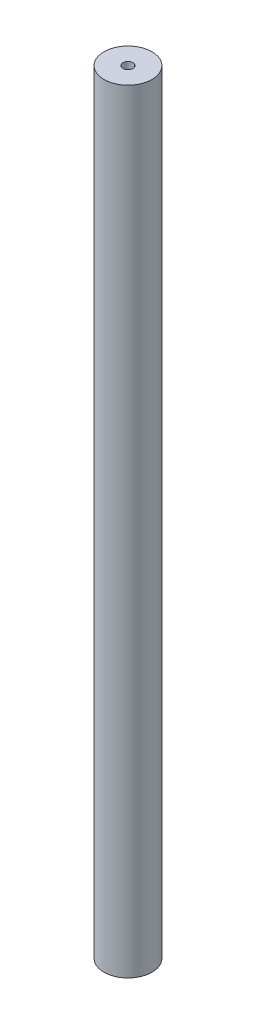
SolidWorks part; units mm, degrees
ref_plane "Front Plane" through (0, 0, 0) normal (0, 0, 1) x (1, 0, 0)
ref_plane "Top Plane" through (0, 0, 0) normal (0, 1, 0) x (1, 0, 0)
ref_plane "Right Plane" through (0, 0, 0) normal (1, 0, 0) x (0, 0, -1)
sketch "Sketch1" plane through (0, 0, 0) normal (0, 1, 0) x (1, 0, 0)
  circle A0 centre (0, 0) radius 10
  dimension "D1" = 20
extrude "Boss-Extrude1" add sketch "Sketch1" along normal mid plane 322.2
hole_wizard "M5x0.8 Tapped Hole1" positions "Sketch2" profile "Sketch3" tap size "M5x0.8" standard "ANSI Metric"
sketch "Sketch2" plane through (0, 161.1, 0) normal (0, 1, 0) x (1, 0, 0)
  point P0 (0, 0)
sketch "Sketch3" plane through (0, 161.1, 0) normal (1, 0, 0) x (0, 0, 1)
  line L0 (0, 0) -> (0, 23.7618)
  line L1 (0, 23.7618) -> (2.1, 22.5)
  line L2 (2.1, 22.5) -> (2.1, 0)
  line L5 (2.1, 0) -> (0, 0)
  line L10 (0, 23.7618) -> (-2.1, 22.5) construction
  line L11 (0, -6.35) -> (0, 107.95) construction
  dimension "Tap Drill Dia." = 4.2
  dimension "Tap Drill Depth" = 22.5
  dimension "Drill Angle" = 118
cosmetic thread "Hole Thread1"
mirror "Mirror1" about plane through (0, 0, 0) normal (0, 1, 0) of "M5x0.8 Tapped Hole1"
